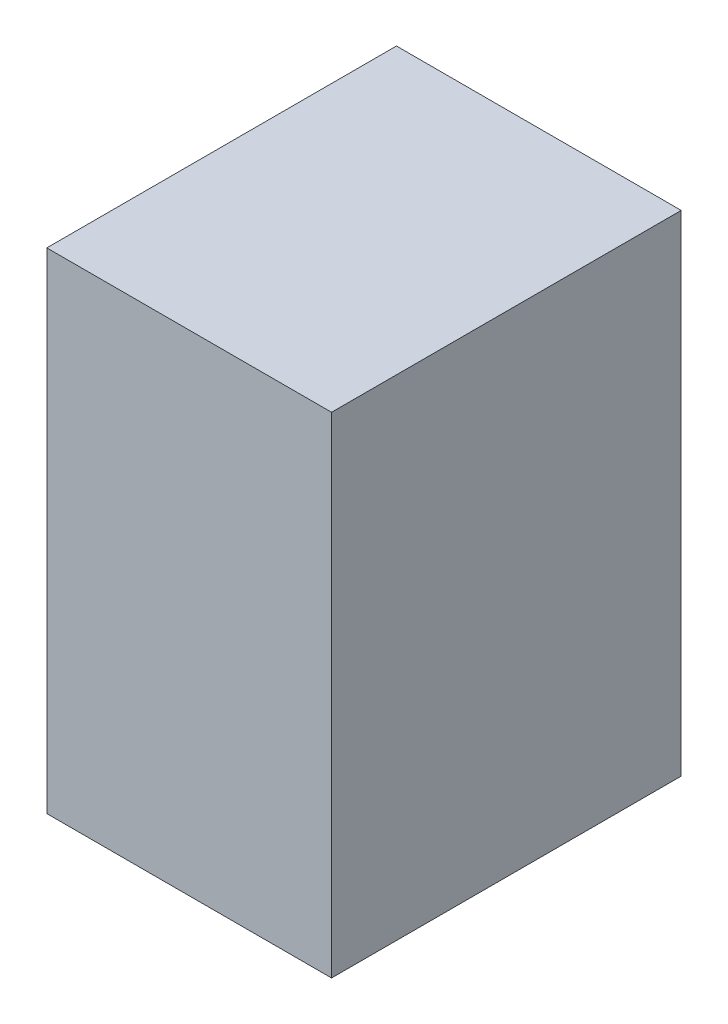
SolidWorks part; units mm, degrees
ref_plane "Front Plane" through (0, 0, 0) normal (0, 0, 1) x (1, 0, 0)
ref_plane "Top Plane" through (0, 0, 0) normal (0, 1, 0) x (1, 0, 0)
ref_plane "Right Plane" through (0, 0, 0) normal (1, 0, 0) x (0, 0, -1)
sketch "Sketch1" plane through (0, 0, 0) normal (0, 1, 0) x (1, 0, 0)
  line L1 (-54.8084, 43.6864) -> (13.1916, 43.6864)
  line L2 (-54.8084, 43.6864) -> (-54.8084, -39.8136)
  line L3 (-54.8084, -39.8136) -> (13.1916, -39.8136)
  line L4 (13.1916, 43.6864) -> (13.1916, -39.8136)
  dimension "D1" = 83.5
  dimension "D2" = 68
extrude "Boss-Extrude1" add sketch "Sketch1" along normal blind 117
